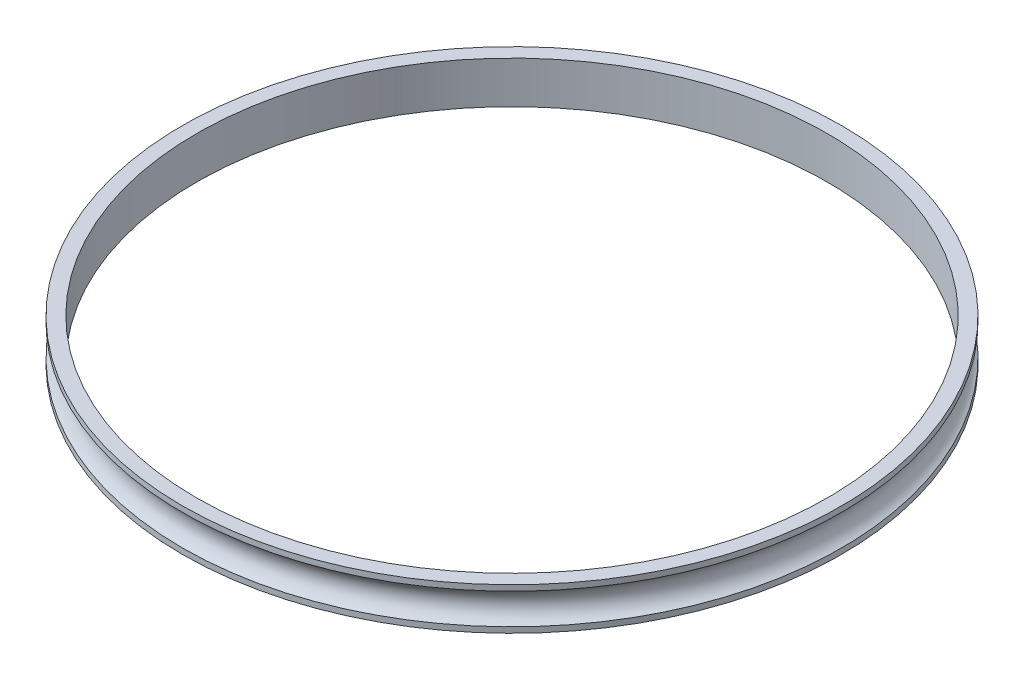
SolidWorks part; units mm, degrees
ref_plane "Front Plane" through (0, 0, 0) normal (0, 0, 1) x (1, 0, 0)
ref_plane "Top Plane" through (0, 0, 0) normal (0, 1, 0) x (1, 0, 0)
ref_plane "Right Plane" through (0, 0, 0) normal (1, 0, 0) x (0, 0, -1)
sketch "Sketch1" plane through (0, 0, 0) normal (0, 1, 0) x (1, 0, 0)
  circle A0 centre (0, 0) radius 45
  circle A1 centre (0, 0) radius 47
  dimension "D1" = 90
  dimension "D2" = 94
extrude "Boss-Extrude1" add sketch "Sketch1" along normal blind 6 contours A0 | A1
sketch "Sketch4" plane through (0, 0, 0) normal (1, 0, 0) x (0, 0, -1)
  line L0 (-47, 6) -> (-47, 0) construction
  line L1 (0, 0) -> (0, 9.2745) construction
  circle A1 centre (-48.2, 3) radius 2.5
  dimension "D1" = 5
  dimension "D2" = 1.2
revolve "Cut-Revolve2" cut sketch "Sketch4" angle 360 about L1
equation "\"inner_diameter\"= 90mm"
equation "\"D1@Sketch1\"=\"inner_diameter\""
equation "\"D2@Sketch1\"=\"inner_diameter\"+4"
